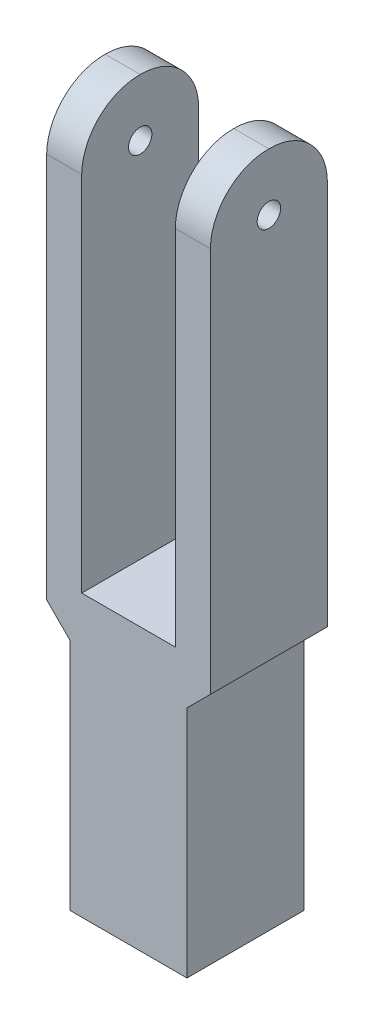
SolidWorks part; units mm, degrees
ref_plane "Front Plane" through (0, 0, 0) normal (0, 0, 1) x (1, 0, 0)
ref_plane "Top Plane" through (0, 0, 0) normal (0, 1, 0) x (1, 0, 0)
ref_plane "Right Plane" through (0, 0, 0) normal (1, 0, 0) x (0, 0, -1)
sketch "Sketch1" plane through (0, 0, 0) normal (0, 1, 0) x (1, 0, 0)
  line L1 (3.5, -2.5) -> (-3.5, -2.5)
  line L2 (3.5, -2.5) -> (3.5, 2.5)
  line L3 (3.5, 2.5) -> (-3.5, 2.5)
  line L4 (-3.5, -2.5) -> (-3.5, 2.5)
  line L5 (3.5, -2.5) -> (-3.5, 2.5) construction
  line L6 (3.5, 2.5) -> (-3.5, -2.5) construction
  point P0 (0, 0)
  dimension "D1" = 7
  dimension "D2" = 5
extrude "Boss-Extrude1" add sketch "Sketch1" along normal blind 30
sketch "Sketch3" plane through (0, 0, 0) normal (0, -1, 0) x (1, 0, 0)
  line L0 (3.5, -2.5) -> (-3.5, -2.5) construction
  line L1 (-3.5, 2.5) -> (-2.5, 2.5)
  line L2 (-3.5, 2.5) -> (-3.5, -2.5)
  line L3 (-3.5, -2.5) -> (-2.5, -2.5)
  line L4 (-2.5, 2.5) -> (-2.5, -2.5)
  line L5 (0, 2.5) -> (0, -2.5) construction
  line L6 (-3.5, 2.5) -> (3.5, 2.5) construction
  line L7 (2.5, 2.5) -> (2.5, -2.5)
  line L8 (3.5, -2.5) -> (2.5, -2.5)
  line L9 (3.5, 2.5) -> (3.5, -2.5)
  line L10 (3.5, 2.5) -> (2.5, 2.5)
  dimension "D1" = 1
extrude "Cut-Extrude1" cut sketch "Sketch3" against normal blind 10
sketch "Sketch4" plane through (0, 30, 0) normal (0, 1, 0) x (1, 0, 0)
  line L0 (3.5, 2.5) -> (-3.5, 2.5) construction
  line L1 (2, -2.5) -> (-2, -2.5)
  line L2 (2, -2.5) -> (2, 2.5)
  line L3 (2, 2.5) -> (-2, 2.5)
  line L4 (-2, -2.5) -> (-2, 2.5)
  line L5 (2, -2.5) -> (-2, 2.5) construction
  line L6 (2, 2.5) -> (-2, -2.5) construction
  point P0 (0, 0)
  dimension "D1" = 4
extrude "Cut-Extrude2" cut sketch "Sketch4" against normal blind 18
sketch "Sketch5" plane through (0, 0, 2.5) normal (0, 0, 1) x (1, 0, 0)
  line L0 (-3.5, 10) -> (-2.5, 10)
  line L1 (-2.5, 10) -> (-3.5, 11)
  line L2 (-3.5, 30) -> (-3.5, 10) construction
  line L3 (-3.5, 11) -> (-3.5, 10)
  line L4 (0, 12) -> (0, 0) construction
  line L5 (-2, 12) -> (2, 12) construction
  line L6 (3.5, 11) -> (3.5, 10)
  line L7 (2.5, 10) -> (3.5, 11)
  line L8 (3.5, 10) -> (2.5, 10)
  dimension "D1" = 1
extrude "Cut-Extrude3" cut sketch "Sketch5" against normal up to next
sketch "Sketch7" plane through (3.5, 0, 0) normal (1, 0, 0) x (0, 0, -1)
  line L0 (-2.5, 30) -> (-2.5, 11) construction
  line L1 (-2.5, 30) -> (2.5, 30) construction
  line L2 (2.5, 30) -> (2.5, 11) construction
  line L3 (-2.5, 27.5) -> (-2.5, 30)
  line L4 (-2.5, 30) -> (2.5, 30)
  line L6 (2.5, 27.5) -> (2.5, 30)
  arc A0 (-2.5, 27.5) -> (0, 29.9478) centre (-0.0261, 27.4739) cw
  arc A1 (0, 29.9478) -> (2.5, 27.5) centre (0.0261, 27.4739) cw
  point P0 (-2.5, 27.5)
  point P5 (2.5, 27.5)
  point P6 (0, 30)
  dimension "D1" = 2.5
extrude "Cut-Extrude5" cut sketch "Sketch7" against normal through all
sketch "Sketch8" plane through (3.5, 0, 0) normal (1, 0, 0) x (0, 0, -1)
  line L0 (-2.5, 27.5) -> (2.5, 27.5) construction
  circle A0 centre (0, 27.5) radius 0.5
  dimension "D1" = 1
extrude "Cut-Extrude6" cut sketch "Sketch8" against normal through all
sketch "Sketch9" plane through (0, 0, 0) normal (0, -1, 0) x (1, 0, 0)
  circle A0 centre (0, 0) radius 1
  dimension "D1" = 2
extrude "Cut-Extrude7" cut sketch "Sketch9" against normal blind 10
